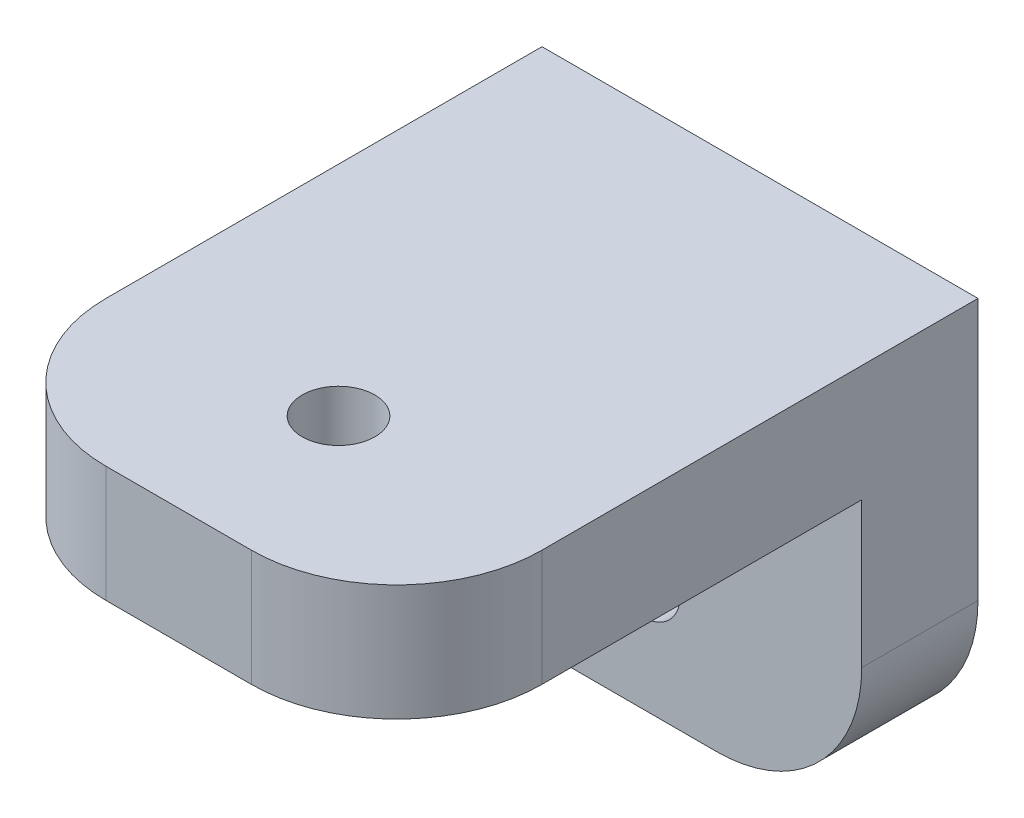
SolidWorks part; units mm, degrees
ref_plane "Front Plane" through (0, 0, 0) normal (0, 0, 1) x (1, 0, 0)
ref_plane "Top Plane" through (0, 0, 0) normal (0, 1, 0) x (1, 0, 0)
ref_plane "Right Plane" through (0, 0, 0) normal (1, 0, 0) x (0, 0, -1)
sketch "Sketch1" plane through (0, 0, 0) normal (0, 1, 0) x (1, 0, 0)
  line L1 (0, 0) -> (30, 0)
  line L2 (0, 0) -> (0, 40)
  line L3 (0, 40) -> (30, 40)
  line L4 (30, 0) -> (30, 40)
  dimension "D1" = 40
  dimension "D2" = 30
extrude "Boss-Extrude1" add sketch "Sketch1" along normal blind 8
sketch "Sketch2" plane through (0, 0, 0) normal (0, -1, 0) x (1, 0, 0)
  line L0 (30, 0) -> (30, -40) construction
  line L1 (0, -40) -> (30, -40)
  line L2 (0, -40) -> (0, -32)
  line L3 (0, -32) -> (30, -32)
  line L4 (30, -40) -> (30, -32)
  dimension "D1" = 8
extrude "Boss-Extrude2" add sketch "Sketch2" along normal blind 20
sketch "Sketch3" plane through (0, 8, 0) normal (0, 1, 0) x (1, 0, 0)
  line L0 (30, 40) -> (0, 40) construction
  line L1 (30, 0) -> (30, 40) construction
  circle A0 centre (15, 11) radius 2.5
  dimension "D3" = 5
  dimension "D1" = 29
  dimension "D2" = 15
extrude "Cut-Extrude1" cut sketch "Sketch3" against normal blind 10
sketch "Sketch4" plane through (0, 0, -40) normal (0, 0, -1) x (-1, 0, 0)
  line L0 (-30, 8) -> (0, 8) construction
  line L1 (0, 8) -> (0, -20) construction
  circle A0 centre (-15, -12) radius 2.5
  dimension "D3" = 5
  dimension "D1" = 20
  dimension "D2" = 15
extrude "Cut-Extrude2" cut sketch "Sketch4" against normal blind 10
fillet "Fillet2" radius 10 4 edges at (30, -20, -36) (0, -20, -36) (0, 4, 0) (30, 4, 0)
